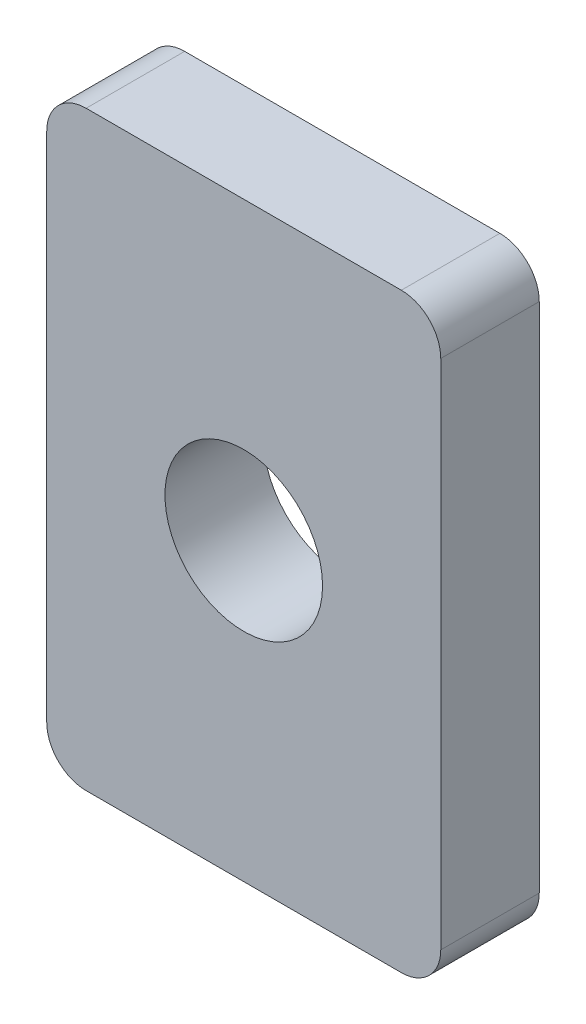
SolidWorks part; units mm, degrees
ref_plane "正面" through (0, 0, 0) normal (0, 0, 1) x (1, 0, 0)
ref_plane "平面" through (0, 0, 0) normal (0, 1, 0) x (1, 0, 0)
ref_plane "右側面" through (0, 0, 0) normal (1, 0, 0) x (0, 0, -1)
sketch "ｽｹｯﾁ1" plane through (0, 0, 0) normal (0, 0, 1) x (1, 0, 0)
  line L1 (-5, 7.5) -> (5, 7.5)
  line L2 (-5, 7.5) -> (-5, -7.5)
  line L3 (-5, -7.5) -> (5, -7.5)
  line L4 (5, 7.5) -> (5, -7.5)
  line L5 (-5, 7.5) -> (5, -7.5) construction
  line L6 (-5, -7.5) -> (5, 7.5) construction
  circle A0 centre (0, 0) radius 2
  point P0 (0, 0)
  dimension "D2" = 5
  dimension "D3" = 4
  dimension "D1" = 15
extrude "ﾎﾞｽ - 押し出し1" add sketch "ｽｹｯﾁ1" along normal blind 2.5
fillet "ﾌｨﾚｯﾄ1" radius 1 4 edges at (5, -7.5, 1.25) (-5, -7.5, 1.25) (-5, 7.5, 1.25) (5, 7.5, 1.25)
